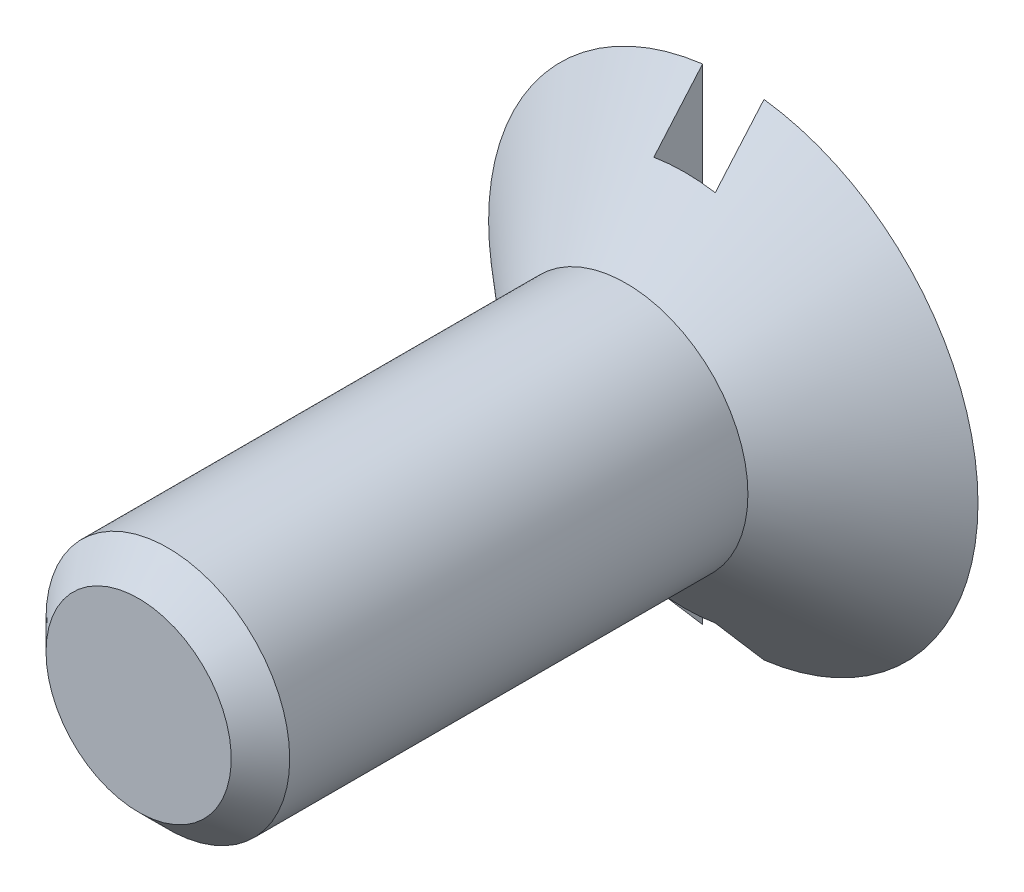
SolidWorks part; units mm, degrees
ref_plane "Front Plane" through (0, 0, 0) normal (0, 0, 1) x (1, 0, 0)
ref_plane "Top Plane" through (0, 0, 0) normal (0, 1, 0) x (1, 0, 0)
ref_plane "Right Plane" through (0, 0, 0) normal (1, 0, 0) x (0, 0, -1)
sketch "Sketch5" plane through (0, 0, 0) normal (0, 1, 0) x (1, 0, 0)
  line L0 (0, 14.732) -> (0, -0.762)
  line L3 (0, 0) -> (0, -0.762) construction
  line L5 (0, 14.732) -> (6.3754, 14.732)
  line L7 (3.175, 0) -> (3.175, 11.938)
  line L8 (0, -0.762) -> (2.413, -0.762)
  line L10 (6.3754, 14.732) -> (3.175, 11.938)
  line L11 (3.175, 0) -> (2.413, -0.762)
  dimension "D3" = 3.175
  dimension "D4" = 2.413
  dimension "D5" = 6.3754
  dimension "D7" = 11.938
revolve "Revolve2" add sketch "Sketch5" angle 360 about L3
sketch "Sketch6" plane through (0, 0, -14.732) normal (0, 0, -1) x (-1, 0, 0)
  line L0 (0, 0) -> (0, -7.2144) construction
  line L1 (0.8001, -6.8132) -> (-0.8001, -6.8132)
  line L2 (-0.8001, -6.8132) -> (-0.8001, 7.6134)
  line L3 (-0.8001, 7.6134) -> (0.8001, 7.6134)
  line L4 (0.8001, 7.6134) -> (0.8001, -6.8132)
  point P6 (0, -6.8132)
  dimension "D1" = 1.6002
extrude "Cut-Extrude2" cut sketch "Sketch6" against normal blind 1.27
